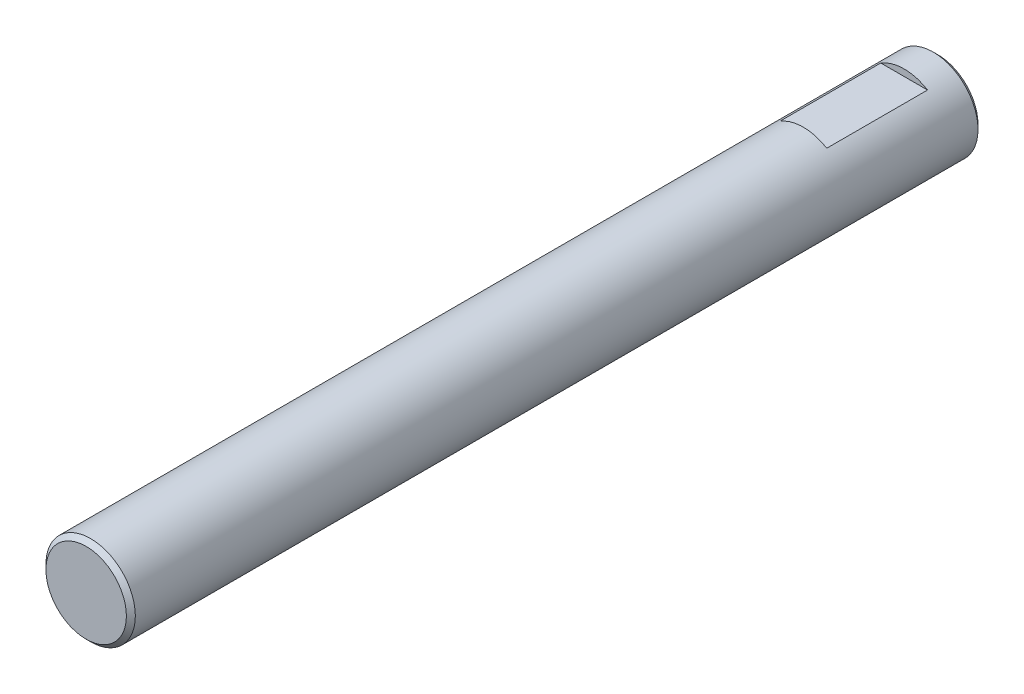
SolidWorks part; units mm, degrees
ref_plane "Front Plane" through (0, 0, 0) normal (0, 0, 1) x (1, 0, 0)
ref_plane "Top Plane" through (0, 0, 0) normal (0, 1, 0) x (1, 0, 0)
ref_plane "Right Plane" through (0, 0, 0) normal (1, 0, 0) x (0, 0, -1)
sketch "Sketch1" plane through (0, 0, 0) normal (0, 0, 1) x (1, 0, 0)
  circle A0 centre (0, 0) radius 1.995
  dimension "D1" = 3.99
extrude "Boss-Extrude1" add sketch "Sketch1" along normal blind 38
sketch "Sketch2" plane through (0, 0, 0) normal (1, 0, 0) x (0, 0, -1)
  line L0 (0, -1.995) -> (0, 1.995) construction
  line L1 (-1.5, 2.6204) -> (-6, 2.6204)
  line L2 (-1.5, 2.6204) -> (-1.5, 1.7)
  line L3 (-1.5, 1.7) -> (-6, 1.7)
  line L4 (-6, 2.6204) -> (-6, 1.7)
  line L5 (-7.2858, 0) -> (2.8383, 0) construction
  line L6 (-6, -2.6204) -> (-6, -1.7)
  line L7 (-1.5, -1.7) -> (-6, -1.7)
  line L8 (-1.5, -2.6204) -> (-1.5, -1.7)
  line L9 (-1.5, -2.6204) -> (-6, -2.6204)
  point P6 (-3.75, 1.7)
  dimension "D1" = 3.75
  dimension "D2" = 4.5
  dimension "D3" = 3.4
extrude "Cut-Extrude1" cut sketch "Sketch2" against normal through all both and the other way through all
chamfer "Chamfer1" distance 0.2 angle 45 2 edges at (1.995, 0, 38) (1.995, 0, 0)
